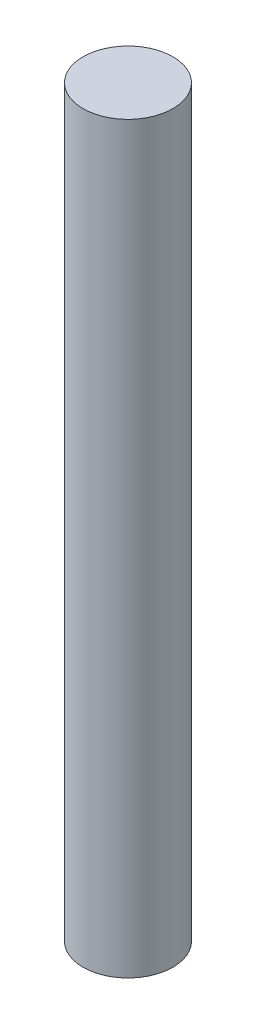
SolidWorks part; units mm, degrees
ref_plane "Front Plane" through (0, 0, 0) normal (0, 0, 1) x (1, 0, 0)
ref_plane "Top Plane" through (0, 0, 0) normal (0, 1, 0) x (1, 0, 0)
ref_plane "Right Plane" through (0, 0, 0) normal (1, 0, 0) x (0, 0, -1)
sketch "Sketch1" plane through (0, 0, 0) normal (0, 1, 0) x (1, 0, 0)
  circle A0 centre (0, 0) radius 1.45
  dimension "D1" = 2.9
extrude "Boss-Extrude1" add sketch "Sketch1" along normal blind 24 contours A0
